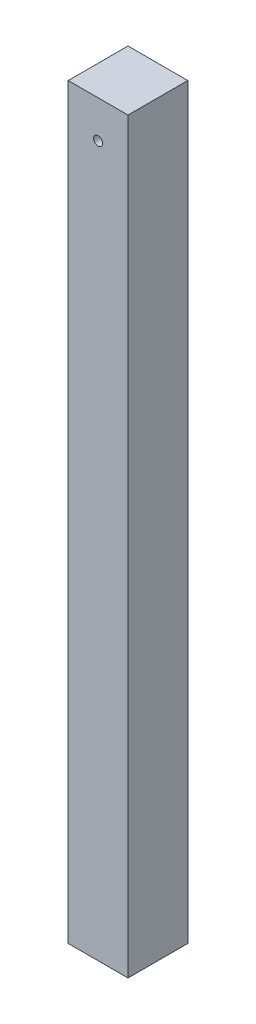
SolidWorks part; units mm, degrees
ref_plane "Ön Düzlem" through (0, 0, 0) normal (0, 0, 1) x (1, 0, 0)
ref_plane "Üst Düzlem" through (0, 0, 0) normal (0, 1, 0) x (1, 0, 0)
ref_plane "Sağ Düzlem" through (0, 0, 0) normal (1, 0, 0) x (0, 0, -1)
sketch "Çizim1" plane through (0, 0, 0) normal (0, 0, 1) x (1, 0, 0)
  line L0 (-40, -500) -> (-40, 500)
  line L1 (-40, -500) -> (40, -500)
  line L2 (-40, 500) -> (40, 500)
  line L3 (40, -500) -> (40, 500)
  line L4 (-40, -500) -> (40, 500) construction
  line L5 (-40, 500) -> (40, -500) construction
  point P1 (0, 0)
  dimension "D1" = 1000
  dimension "D2" = 80
extrude "Yükseklik-Ekstrüzyon1" add sketch "Çizim1" against normal blind 80
sketch "Çizim2" plane through (0, 0, 0) normal (0, 0, 1) x (1, 0, 0)
  line L0 (40, 500) -> (-40, 500) construction
  circle A0 centre (0, 450) radius 6
  point P2 (0, 500)
  dimension "D1" = 12
  dimension "D2" = 50
extrude "Kes-Ekstrüzyon1" cut sketch "Çizim2" against normal up to next
